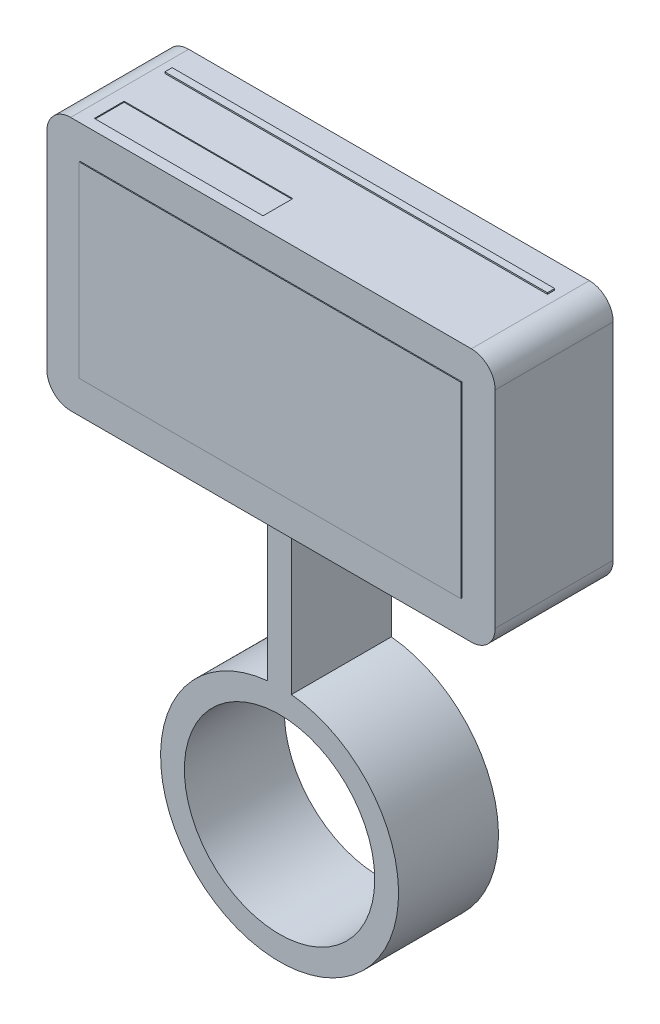
SolidWorks part; units mm, degrees
ref_plane "Front Plane" through (0, 0, 0) normal (0, 0, 1) x (1, 0, 0)
ref_plane "Top Plane" through (0, 0, 0) normal (0, 1, 0) x (1, 0, 0)
ref_plane "Right Plane" through (0, 0, 0) normal (1, 0, 0) x (0, 0, -1)
sketch "Sketch1" plane through (0, 0, 0) normal (0, 0, 1) x (1, 0, 0)
  line L0 (0, -20) -> (0, 35.298) construction
  line L1 (-2.5, 4.8747) -> (-2.5, 35.298)
  line L2 (-2.5, 35.298) -> (2.5, 35.298)
  line L3 (2.5, 35.298) -> (2.5, 4.8747)
  circle A0 centre (0, -20) radius 20
  arc A1 (-2.5, 4.8747) -> (2.5, 4.8747) centre (0, -20) ccw
  dimension "D1" = 40
  dimension "D2" = 50
  dimension "D3" = 2.5
  dimension "D4" = 2.5
extrude "Boss-Extrude1" add sketch "Sketch1" along normal blind 21
sketch "Sketch2" plane through (0, 0, 0) normal (0, 0, -1) x (-1, 0, 0)
  line L1 (-47.1007, 88.4984) -> (47.1007, 88.4984)
  line L2 (-47.1007, 88.4984) -> (-47.1007, 35.1153)
  line L3 (-47.1007, 35.1153) -> (47.1007, 35.1153)
  line L4 (47.1007, 88.4984) -> (47.1007, 35.1153)
  line L5 (-47.1007, 88.4984) -> (47.1007, 35.1153) construction
  line L6 (-47.1007, 35.1153) -> (47.1007, 88.4984) construction
  point P0 (0, 61.8068)
extrude "Boss-Extrude2" add sketch "Sketch2" against normal blind 23 and the other way blind 2
sketch "Sketch3" plane through (0, 0, -2) normal (0, 0, -1) x (-1, 0, 0)
  circle A0 centre (0, 62.4807) radius 21.4662
  circle A1 centre (0, 62.4807) radius 16.5834
extrude "Boss-Extrude3" add sketch "Sketch3" along normal blind 3
sketch "Sketch4" plane through (0, 0, 0) normal (1, 0, 0) x (0, 0, -1)
  line L0 (5, 62.4807) -> (49.0133, 62.4807) construction
  line L1 (5, 41.0144) -> (5, 83.9469) construction
  line L3 (5, 79.0641) -> (5, 62.4807)
  line L4 (5, 62.4807) -> (9.3573, 62.4807)
  arc A0 (5, 79.0641) -> (9.3573, 62.4807) centre (-33.3106, 60.1339) cw
revolve "Revolve2" add sketch "Sketch4" angle 360 about L0
sketch "Sketch5" plane through (0, 0, -2) normal (0, 0, -1) x (-1, 0, 0)
  line L1 (-41.6571, 82.8695) -> (-31.0848, 82.8695)
  line L2 (-41.6571, 82.8695) -> (-41.6571, 73.2165)
  line L3 (-41.6571, 73.2165) -> (-31.0848, 73.2165)
  line L4 (-31.0848, 82.8695) -> (-31.0848, 73.2165)
  line L5 (-41.6571, 82.8695) -> (-31.0848, 73.2165) construction
  line L6 (-41.6571, 73.2165) -> (-31.0848, 82.8695) construction
  circle A0 centre (31.253, 84.4983) radius 1.6732
  circle A1 centre (40.4463, 84.4983) radius 1.7504
  point P0 (-36.3709, 78.043)
extrude "Boss-Extrude4" add sketch "Sketch5" along normal blind 1
sketch "Sketch6" plane through (0, 0, -3) normal (0, 0, -1) x (-1, 0, 0)
  circle A0 centre (31.253, 84.4983) radius 1.1453
extrude "Cut-Extrude1" cut sketch "Sketch6" against normal blind 0.5
fillet "Fillet1" radius 5 4 edges at (-47.1007, 35.1153, 10.5) (47.1007, 35.1153, 10.5) (-47.1007, 88.4984, 10.5) (47.1007, 88.4984, 10.5)
sketch "Sketch7" plane through (0, 88.4984, 0) normal (0, 1, 0) x (1, 0, 0)
  line L2 (-40.1902, -17.442) -> (-40.1902, -18.9701)
  line L4 (40.1902, -17.442) -> (40.1902, -18.9701)
  line L7 (-40.1902, -4.9112) -> (40.1902, -4.9112)
  line L8 (-40.1902, -4.9112) -> (-40.1902, -3.383)
  line L9 (-40.1902, -3.383) -> (40.1902, -3.383)
  line L10 (40.1902, -4.9112) -> (40.1902, -3.383)
  line L11 (-40.1902, -4.9112) -> (40.1902, -3.383) construction
  line L12 (-40.1902, -3.383) -> (40.1902, -4.9112) construction
  point P0 (0, -18.2061)
  point P5 (0, -4.1471)
extrude "Boss-Extrude5" add sketch "Sketch7" along normal blind 0.3 contours L7 L10 L9 L8
sketch "Sketch8" plane through (0, 88.4984, 0) normal (0, 1, 0) x (1, 0, 0)
  line L1 (-39.4261, -14.2329) -> (-3.9732, -14.2329)
  line L2 (-39.4261, -14.2329) -> (-39.4261, -20.4983)
  line L3 (-39.4261, -20.4983) -> (-3.9732, -20.4983)
  line L4 (-3.9732, -14.2329) -> (-3.9732, -20.4983)
extrude "Cut-Extrude2" cut sketch "Sketch8" against normal blind 0.2
sketch "Sketch9" plane through (0, 0, 23) normal (0, 0, 1) x (1, 0, 0)
  line L0 (40.1007, 81.4984) -> (-40.1007, 81.4984)
  line L1 (-40.1007, 81.4984) -> (-40.1007, 42.1153)
  line L2 (-40.1007, 42.1153) -> (40.1007, 42.1153)
  line L3 (40.1007, 42.1153) -> (40.1007, 81.4984)
  line L4 (-47.1007, 83.4984) -> (-47.1007, 40.1153)
  line L5 (-42.1007, 35.1153) -> (42.1007, 35.1153)
  line L6 (47.1007, 40.1153) -> (47.1007, 83.4984)
  line L7 (42.1007, 88.4984) -> (-42.1007, 88.4984)
  line L8 (-47.1007, 83.4984) -> (-47.1007, 40.1153)
  line L9 (-42.1007, 35.1153) -> (42.1007, 35.1153)
  line L10 (47.1007, 40.1153) -> (47.1007, 83.4984)
  line L11 (42.1007, 88.4984) -> (-42.1007, 88.4984)
  arc A0 (-40.1007, 81.4984) -> (-40.1007, 81.4984) centre (-40.1007, 81.4984) ccw
  arc A1 (-40.1007, 42.1153) -> (-40.1007, 42.1153) centre (-40.1007, 42.1153) ccw
  arc A2 (40.1007, 42.1153) -> (40.1007, 42.1153) centre (40.1007, 42.1153) ccw
  arc A3 (40.1007, 81.4984) -> (40.1007, 81.4984) centre (40.1007, 81.4984) ccw
  arc A4 (-47.1007, 40.1153) -> (-42.1007, 35.1153) centre (-42.1007, 40.1153) ccw
  arc A5 (42.1007, 35.1153) -> (47.1007, 40.1153) centre (42.1007, 40.1153) ccw
  arc A6 (47.1007, 83.4984) -> (42.1007, 88.4984) centre (42.1007, 83.4984) ccw
  arc A7 (-42.1007, 88.4984) -> (-47.1007, 83.4984) centre (-42.1007, 83.4984) ccw
  arc A8 (-47.1007, 40.1153) -> (-42.1007, 35.1153) centre (-42.1007, 40.1153) ccw
  arc A9 (42.1007, 35.1153) -> (47.1007, 40.1153) centre (42.1007, 40.1153) ccw
  arc A10 (47.1007, 83.4984) -> (42.1007, 88.4984) centre (42.1007, 83.4984) ccw
  arc A11 (-42.1007, 88.4984) -> (-47.1007, 83.4984) centre (-42.1007, 83.4984) ccw
  dimension "D1" = 0
  dimension "D2" = 7
extrude "Cut-Extrude3" cut sketch "Sketch9" against normal blind 0.2
